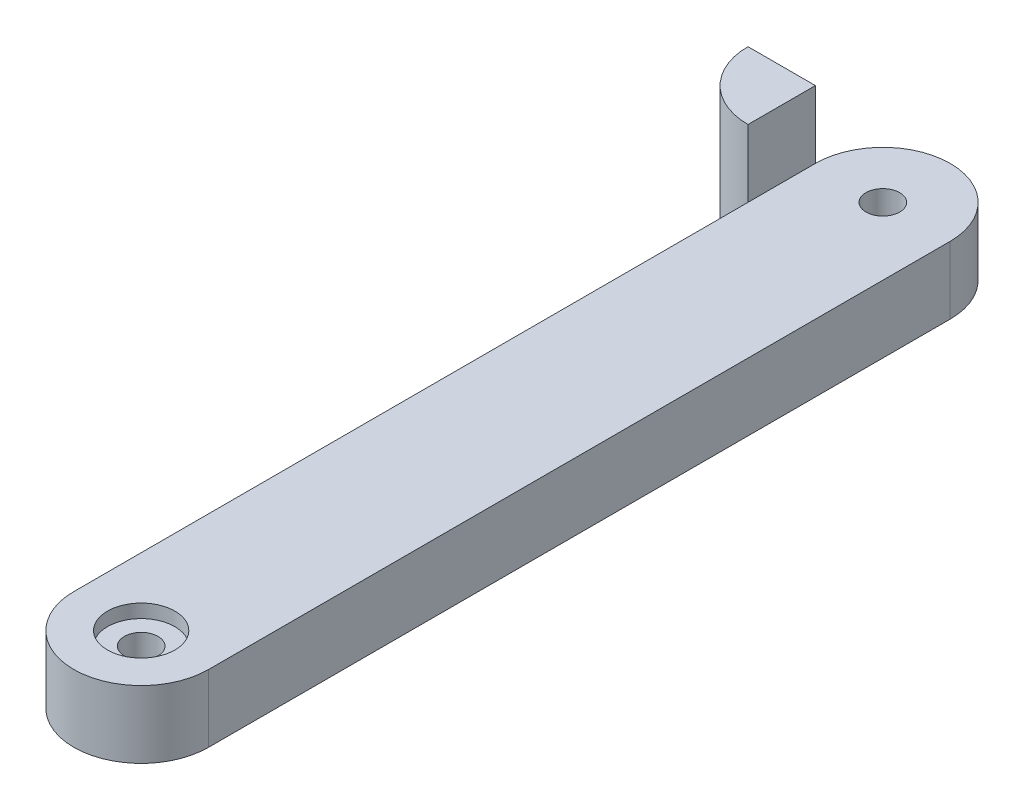
SolidWorks part; units mm, degrees
ref_plane "Front Plane" through (0, 0, 0) normal (0, 0, 1) x (1, 0, 0)
ref_plane "Top Plane" through (0, 0, 0) normal (0, 1, 0) x (1, 0, 0)
ref_plane "Right Plane" through (0, 0, 0) normal (1, 0, 0) x (0, 0, -1)
sketch "Sketch1" plane through (0, 0, 0) normal (0, 1, 0) x (1, 0, 0)
  line L1 (-10, 0) -> (10, 0)
  line L2 (-10, 0) -> (-10, 110)
  line L3 (-10, 110) -> (10, 110)
  line L4 (10, 0) -> (10, 110)
  circle A0 centre (0, 0) radius 10
  circle A1 centre (0, 110) radius 10
  dimension "D1" = 20
  dimension "D2" = 110
extrude "Boss-Extrude2" add sketch "Sketch1" along normal blind 10 contours L3 A1 | L3 A1 | A1 L2 A0 L4 | L1 A0 | L1 A0
sketch "Sketch2" plane through (0, 10, 0) normal (0, 1, 0) x (1, 0, 0)
  circle A0 centre (0, 0) radius 2.5
  circle A1 centre (0, 110) radius 2.5
extrude "Cut-Extrude1" cut sketch "Sketch2" against normal blind 10
sketch "Sketch3" plane through (-10, 0, 0) normal (-1, 0, 0) x (0, 0, 1)
  line L1 (0, 0) -> (-110, 0) construction
  line L2 (-110, 10) -> (-100, 10)
  line L3 (-110, 10) -> (-110, 0)
  line L4 (-110, 0) -> (-100, 0)
  line L5 (-100, 10) -> (-100, 0)
  dimension "D1" = 10
revolve "Revolve1" add sketch "Sketch3" angle 90 about L3
sketch "Sketch4" plane through (0, 10, 0) normal (0, 1, 0) x (1, 0, 0)
  line L0 (-10, 110) -> (-10, 100)
  line L1 (-10, 100) -> (-20, 110)
  line L2 (-20, 110) -> (-10, 110)
extrude "Boss-Extrude3" add sketch "Sketch4" along normal blind 10
sketch "Sketch5" plane through (-10, 0, 0) normal (1, 0, 0) x (0, 0, -1)
  line L0 (112.5, 10) -> (107.5, 10) construction
  line L1 (100, 20) -> (110, 20)
  line L2 (100, 20) -> (100, 10)
  line L3 (100, 10) -> (110, 10)
  line L4 (110, 20) -> (110, 10)
revolve "Revolve2" add sketch "Sketch5" angle 90 about L4
sketch "Sketch7" plane through (0, 10, 0) normal (0, 1, 0) x (1, 0, 0)
  circle A0 centre (0, 0) radius 5
extrude "Cut-Extrude2" cut sketch "Sketch7" against normal blind 2 contours A0
sketch "Sketch8" plane through (0, 0, 0) normal (0, -1, 0) x (1, 0, 0)
  circle A0 centre (0, -110) radius 5
extrude "Cut-Extrude3" cut sketch "Sketch8" against normal blind 2
